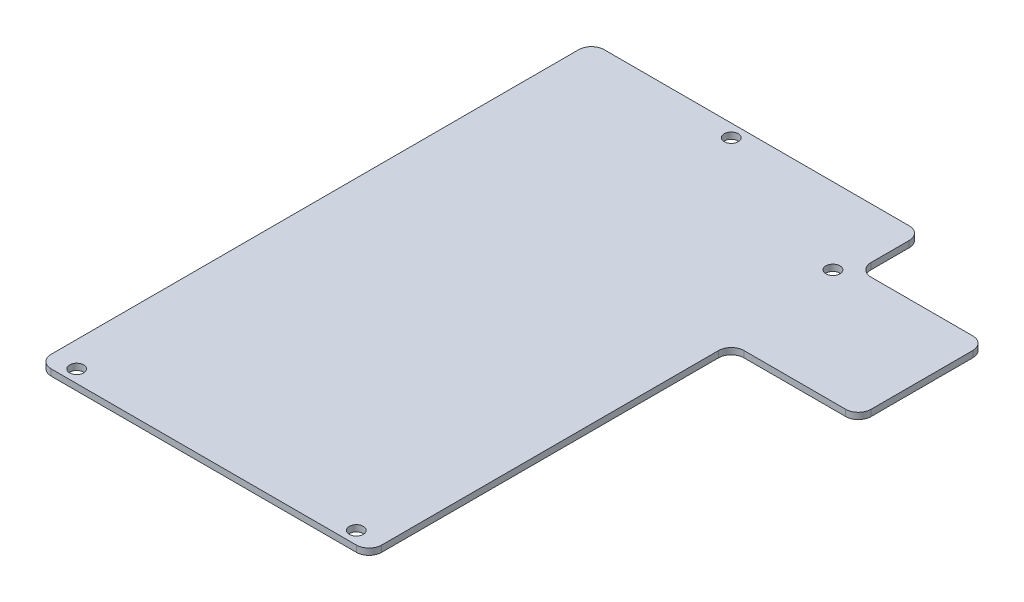
SolidWorks part; units mm, degrees
ref_plane "Front Plane" through (0, 0, 0) normal (0, 0, 1) x (1, 0, 0)
ref_plane "Top Plane" through (0, 0, 0) normal (0, 1, 0) x (1, 0, 0)
ref_plane "Right Plane" through (0, 0, 0) normal (1, 0, 0) x (0, 0, -1)
sketch "Sketch1" plane through (0, 0, 0) normal (0, 1, 0) x (1, 0, 0)
  line L0 (52, 77) -> (52, 87)
  line L1 (0, 0) -> (52, 0)
  line L2 (0, 0) -> (0, 87)
  line L3 (0, 87) -> (52, 87)
  line L4 (52, 0) -> (52, 57)
  line L5 (52, 77) -> (72, 77)
  line L6 (52, 57) -> (72, 57)
  line L7 (72, 77) -> (72, 57)
  dimension "D1" = 52
  dimension "D2" = 87
  dimension "D3" = 20
  dimension "D4" = 20
  dimension "D5" = 10
extrude "Boss-Extrude1" add sketch "Sketch1" along normal blind 1
sketch "Sketch2" plane through (0, 1, 0) normal (0, 1, 0) x (1, 0, 0)
  line L0 (0, 0) -> (52, 0) construction
  line L1 (0, 87) -> (0, 0) construction
  line L2 (52, 0) -> (52, 57) construction
  line L3 (52, 87) -> (0, 87) construction
  line L4 (72, 77) -> (52, 77) construction
  line L5 (52, 77) -> (52, 87) construction
  circle A0 centre (4, 2) radius 1.1
  circle A1 centre (48, 2) radius 1.1
  circle A2 centre (24, 85) radius 1.1
  circle A3 centre (50, 75) radius 1.1
  dimension "D1" = 2
  dimension "D5" = 2
  dimension "D7" = 2
  dimension "D9" = 2.2
  dimension "D2" = 2
  dimension "D3" = 4
  dimension "D4" = 4
  dimension "D6" = 24
  dimension "D8" = 2
extrude "Cut-Extrude1" cut sketch "Sketch2" against normal blind 4
fillet "Fillet1" radius 2 8 edges at (0, 0.5, -87) (52, 0.5, -87) (52, 0.5, -77) (72, 0.5, -77) (72, 0.5, -57) (52, 0.5, -57) (52, 0.5, 0) (0, 0.5, 0)
